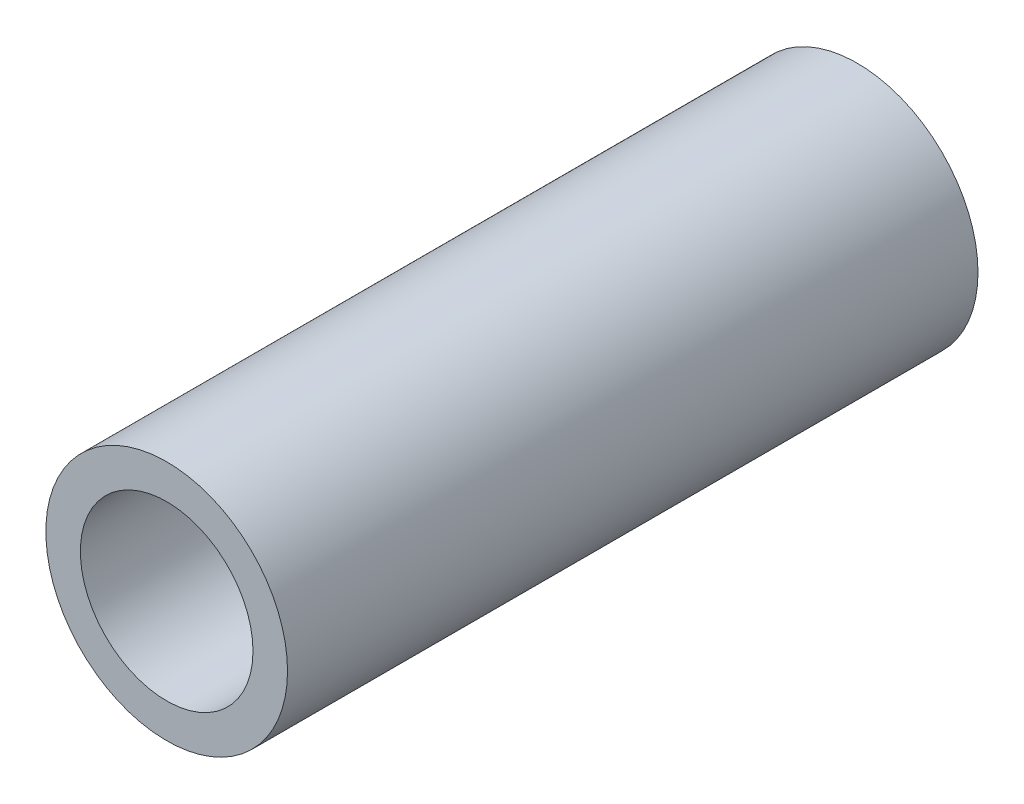
SolidWorks part; units mm, degrees
ref_plane "Plano frontal" through (0, 0, 0) normal (0, 0, 1) x (1, 0, 0)
ref_plane "Plano superior" through (0, 0, 0) normal (0, 1, 0) x (1, 0, 0)
ref_plane "Plano direito" through (0, 0, 0) normal (1, 0, 0) x (0, 0, -1)
sketch "Esboço1" plane through (0, 0, 0) normal (0, 0, 1) x (1, 0, 0)
  circle A0 centre (0, 0) radius 2.5
  circle A1 centre (0, 0) radius 3.5
  dimension "D1" = 5
  dimension "D2" = 7
extrude "Ressalto-extrusão1" add sketch "Esboço1" along normal mid plane 20
